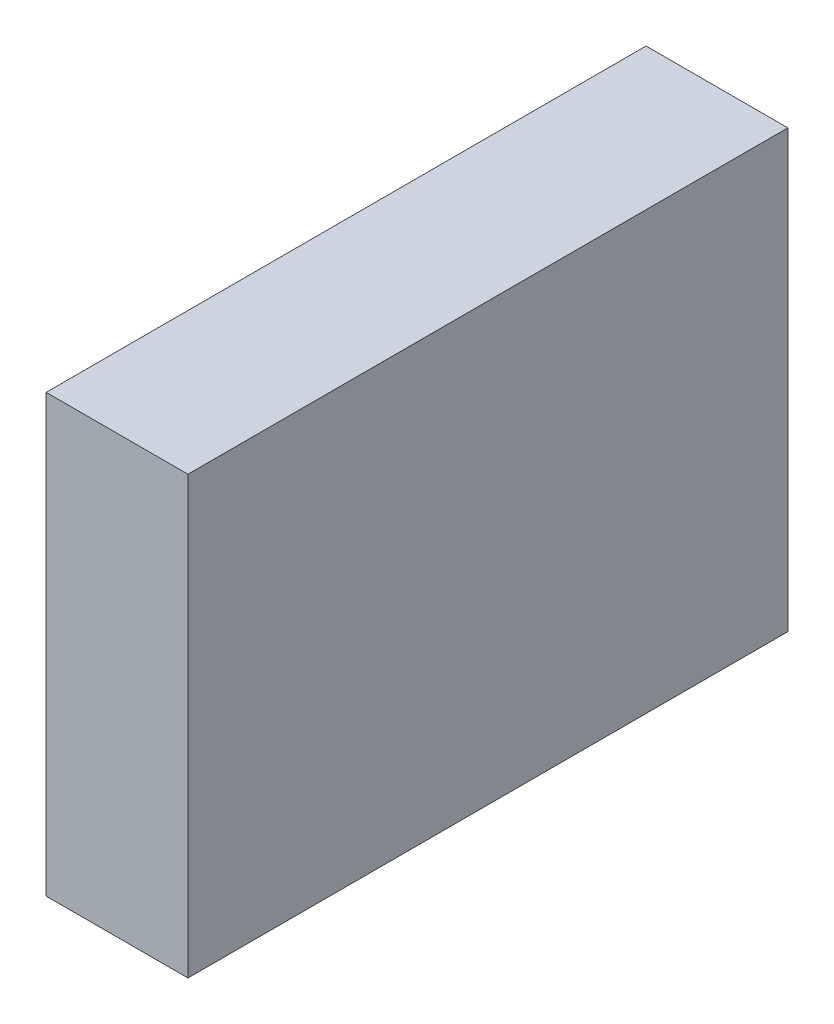
SolidWorks part; units mm, degrees
material "AISI 316 Stainless Steel Sheet (SS)"
ref_plane "Front Plane" through (0, 0, 0) normal (0, 0, 1) x (1, 0, 0)
ref_plane "Top Plane" through (0, 0, 0) normal (0, 1, 0) x (1, 0, 0)
ref_plane "Right Plane" through (0, 0, 0) normal (1, 0, 0) x (0, 0, -1)
sketch "Sketch1" plane through (0, 0, 0) normal (0, 0, 1) x (1, 0, 0)
  line L1 (368.4665, 278) -> (381.4665, 278)
  line L2 (368.4665, 278) -> (368.4665, 238)
  line L3 (368.4665, 238) -> (381.4665, 238)
  line L4 (381.4665, 278) -> (381.4665, 238)
  dimension "D1" = 13
  dimension "D2" = 40
  dimension "D3" = 35
  dimension "D4" = 38
extrude "Boss-Extrude1" add sketch "Sketch1" along normal blind 55
